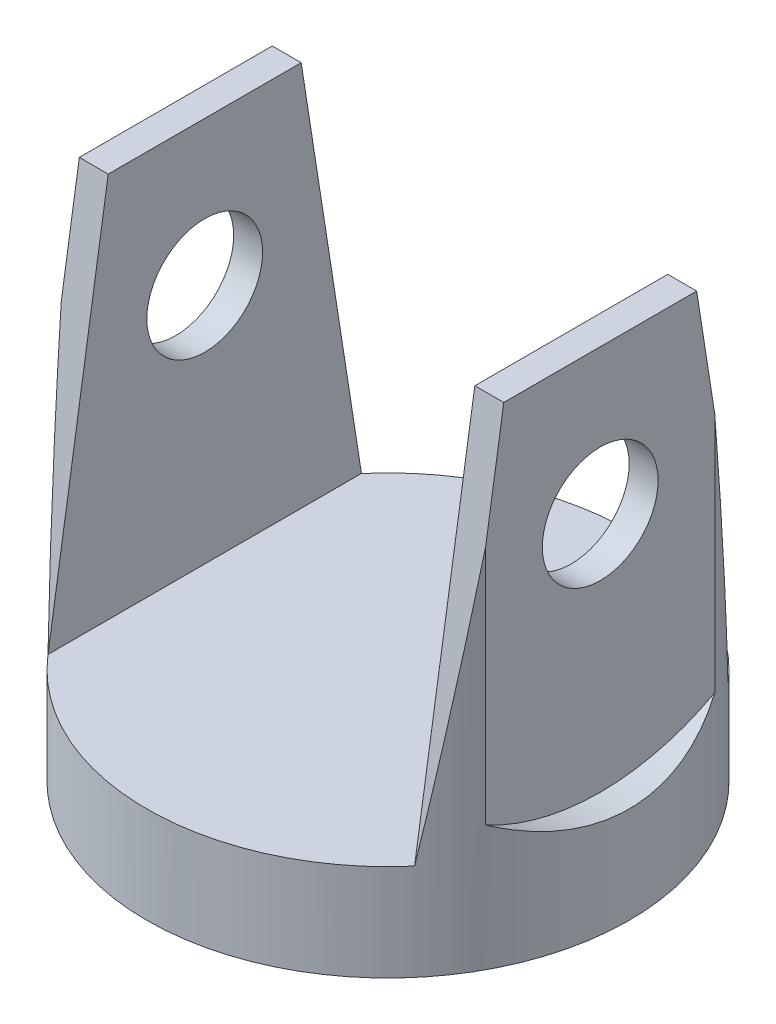
SolidWorks part; units mm, degrees
ref_plane "Front Plane" through (0, 0, 0) normal (0, 0, 1) x (1, 0, 0)
ref_plane "Top Plane" through (0, 0, 0) normal (0, 1, 0) x (1, 0, 0)
ref_plane "Right Plane" through (0, 0, 0) normal (1, 0, 0) x (0, 0, -1)
sketch "Sketch1" plane through (0, 0, 0) normal (0, 1, 0) x (1, 0, 0)
  circle A0 centre (0, 0) radius 125
  dimension "D1" = 250
extrude "Boss-Extrude1" add sketch "Sketch1" along normal blind 250
sketch "Sketch3" plane through (0, 250, 0) normal (0, 1, 0) x (1, 0, 0)
  line L1 (-95, 125) -> (95, 125)
  line L2 (-95, 125) -> (-95, -125)
  line L3 (-95, -125) -> (95, -125)
  line L4 (95, 125) -> (95, -125)
  line L5 (-95, 125) -> (95, -125) construction
  line L6 (-95, -125) -> (95, 125) construction
  circle A0 centre (0, 0) radius 125 construction
  point P0 (0, 0)
  dimension "D1" = 190
extrude "Cut-Extrude1" cut sketch "Sketch3" against normal blind 200
sketch "Sketch4" plane through (-95, 0, 0) normal (1, 0, 0) x (0, 0, -1)
  line L0 (-81.2404, 50) -> (-50, 250)
  line L2 (81.2404, 50) -> (50, 250)
  line L3 (-81.2404, 50) -> (81.2404, 50)
  line L4 (81.2404, 250) -> (-81.2404, 250) construction
  line L5 (81.2404, 250) -> (-81.2404, 250) construction
  line L6 (-50, 250) -> (-81.2404, 250)
  line L7 (-81.2404, 250) -> (-81.2404, 50)
  line L8 (50, 250) -> (81.2404, 250)
  line L9 (81.2404, 250) -> (81.2404, 50)
  point P3 (0, 250)
  point P11 (0, 250)
  line M1 (81.2404, 250) -> (-81.2404, 250)
  line M2 (-81.2404, 250) -> (-81.2404, 50)
  line M4 (81.2404, 50) -> (81.2404, 250)
  dimension "D1" = 50
  dimension "D2" = 50
extrude "Cut-Extrude3" cut sketch "Sketch4" against normal through all both and the other way through all contours L0 M2 M1 | L2 M4 M1
ref_plane "Plane1" through (-170, 0, 0) normal (1, 0, 0) x (0, 0, -1)
sketch "Sketch6" plane through (-170, 0, 0) normal (1, 0, 0) x (0, 0, -1)
  line L0 (50, 250) -> (-50, 250) construction
  circle A0 centre (0, 175) radius 125
  dimension "D1" = 250
  dimension "D2" = 75
ref_plane "Plane2" through (170, 0, 0) normal (-1, 0, 0) x (0, 0, 1)
sketch "Sketch7" plane through (170, 0, 0) normal (-1, 0, 0) x (0, 0, 1)
  circle A0 centre (0, 175) radius 125
  dimension "D1" = 250
sketch "Sketch8" plane through (-95, 0, 0) normal (1, 0, 0) x (0, 0, -1)
  line L0 (50, 250) -> (-50, 250) construction
  circle A0 centre (0, 175) radius 30
  dimension "D1" = 60
  dimension "D2" = 75
extrude "Cut-Extrude4" cut sketch "Sketch8" against normal through all both and the other way through all
extrude "Cut-Extrude8" cut sketch "Sketch6" along normal blind 60
extrude "Cut-Extrude9" cut sketch "Sketch7" along normal blind 60
sketch "Sketch9" plane through (0, 0, 0) normal (0, -1, 0) x (1, 0, 0)
  circle A0 centre (0, 0) radius 59.95
  dimension "D1" = 119.9
extrude "Boss-Extrude2" add sketch "Sketch9" along normal blind 20
